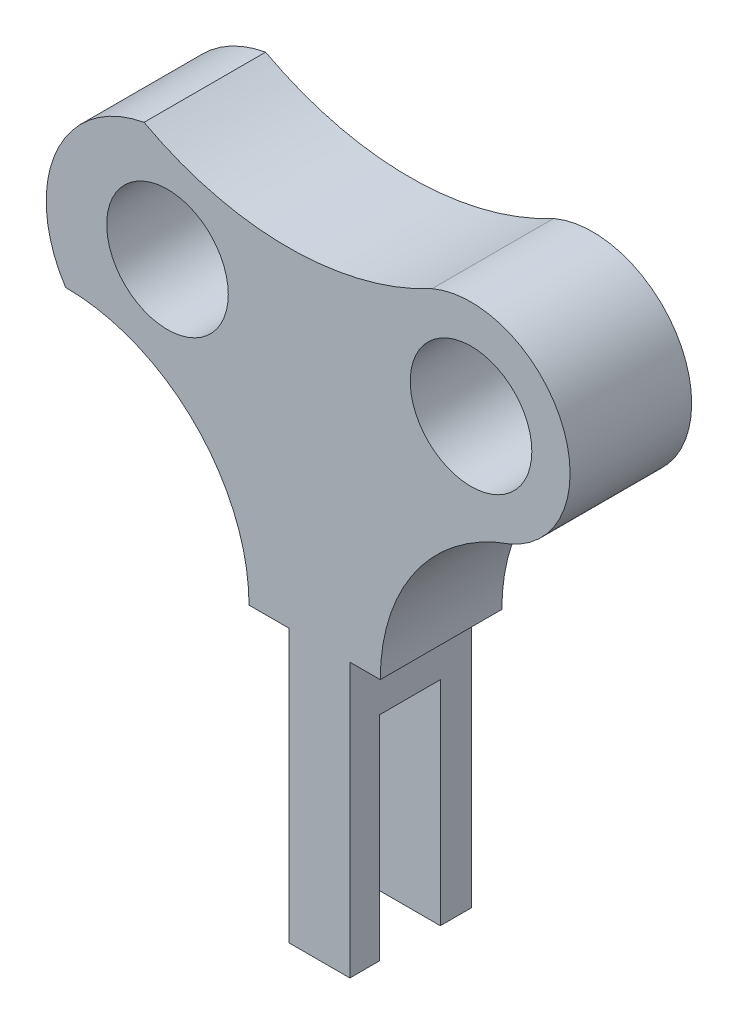
SolidWorks part; units mm, degrees
ref_plane "Front Plane" through (0, 0, 0) normal (0, 0, 1) x (1, 0, 0)
ref_plane "Top Plane" through (0, 0, 0) normal (0, 1, 0) x (1, 0, 0)
ref_plane "Right Plane" through (0, 0, 0) normal (1, 0, 0) x (0, 0, -1)
sketch "Sketch21" plane through (0, 0, 0) normal (0, 0, 1) x (1, 0, 0)
  line L0 (54.893, 39.6894) -> (64.893, 39.6894)
  line L1 (64.893, 39.6894) -> (64.893, 84.6894)
  line L2 (64.893, 84.6894) -> (69.893, 84.6894)
  line L3 (54.893, 39.6894) -> (54.893, 84.5072)
  line L4 (54.893, 84.5072) -> (48.3086, 84.5072)
  line L7 (54.893, 84.5072) -> (34.893, 84.5072) construction
  line L8 (34.893, 84.5072) -> (34.893, 127.0509) construction
  circle A0 centre (84.8246, 129.6671) radius 10
  circle A1 centre (34.893, 127.0509) radius 10
  arc A6 (48.3086, 84.5072) -> (18.1327, 114.6832) centre (18.1327, 84.5072) ccw
  arc A8 (69.893, 84.6894) -> (91.2266, 114.6832) centre (101.6446, 84.6894) cw
  arc A9 (91.2266, 114.6832) -> (78.4225, 144.6509) centre (84.8246, 129.6671) ccw
  arc A11 (18.1327, 114.6832) -> (31.0368, 144.6509) centre (34.5197, 125.3891) cw
  arc A12 (31.0368, 144.6509) -> (78.4225, 144.6509) centre (54.7297, 188.681) ccw
  dimension "D5" = 20
  dimension "D7" = 20
  dimension "D4" = 50
  dimension "D1" = 10
  dimension "D2" = 45
  dimension "D3" = 5
  dimension "D6" = 20
  dimension "D10" = 50
extrude "Boss-Extrude20" add sketch "Sketch21" along normal blind 20
sketch "Sketch24" plane through (54.893, 0, 0) normal (-1, 0, 0) x (0, 0, 1)
  line L0 (0, 39.6894) -> (5.1157, 39.6894) construction
  line L1 (20, 39.6894) -> (0, 39.6894) construction
  line L2 (20, 39.6894) -> (15.1347, 39.6894)
  line L3 (15.1347, 39.6894) -> (15.1347, 74.7423)
  line L4 (15.1347, 74.7423) -> (5.1157, 74.7423)
  line L5 (5.1157, 74.7423) -> (5.1157, 39.6894)
  line L6 (5.1157, 39.6894) -> (15.1347, 39.6894)
  line M6 (0, 39.6894) -> (20, 39.6894)
extrude "Cut-Extrude10" cut sketch "Sketch24" against normal blind 20 contours L4 L5 L3 M6
